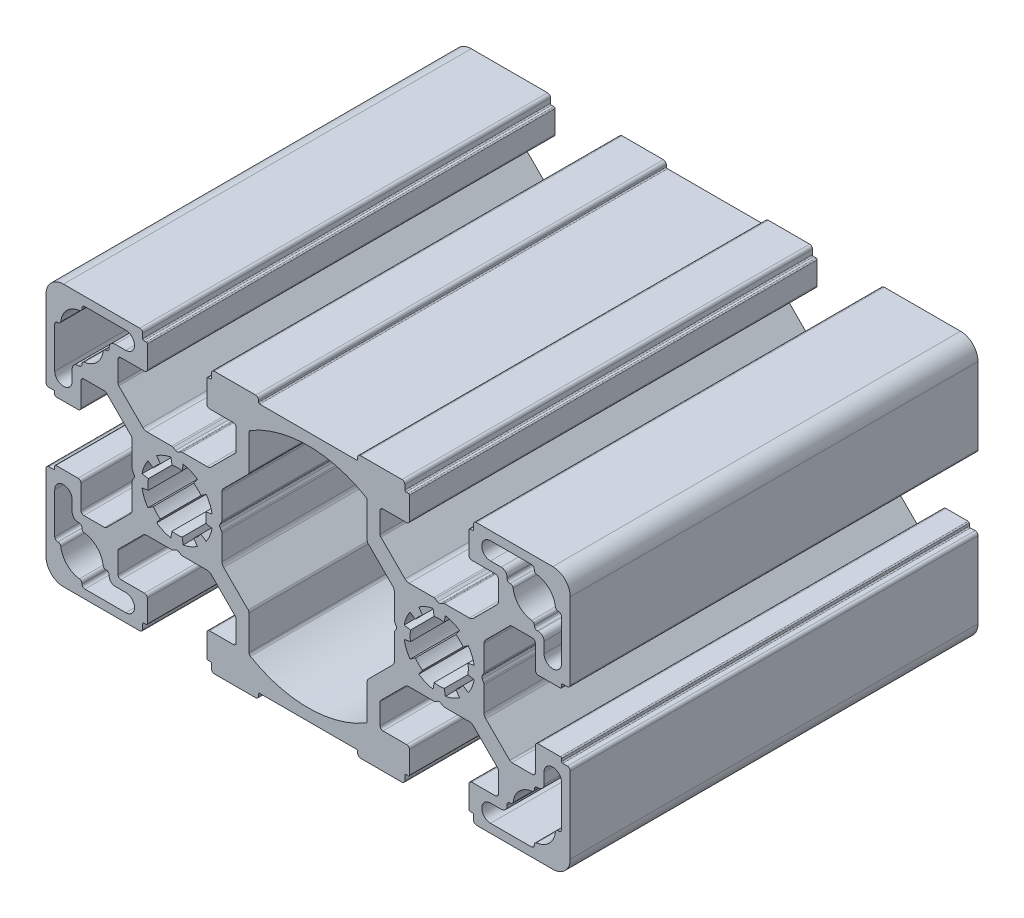
SolidWorks part; units mm, degrees
material "1060 Сплав"
ref_plane "Спереди" through (0, 0, 0) normal (0, 0, 1) x (1, 0, 0)
ref_plane "Сверху" through (0, 0, 0) normal (0, 1, 0) x (1, 0, 0)
ref_plane "Справа" through (0, 0, 0) normal (1, 0, 0) x (0, 0, -1)
sketch "Эскиз1" plane through (0, 0, 0) normal (0, 0, 1) x (1, 0, 0)
  line L0 (-48.4414, 51.0481) -> (-48.4414, 44.0311)
  line L1 (-43.2664, 14.2231) -> (-36.2493, 14.2231)
  line L2 (-35.1419, 36.1522) -> (-35.1419, 40.3881)
  line L3 (-21.8414, 51.7231) -> (-17.7914, 51.7231)
  line L4 (-15.0914, 49.4623) -> (-15.0914, 45.6589)
  line L5 (-17.2012, 43.3419) -> (-15.2378, 45.3054)
  line L6 (-34.8271, 34.9731) -> (-35.0594, 34.5709)
  line L7 (-30.3093, 39.3189) -> (-30.9402, 40.2199)
  line L8 (-43.9414, 40.8231) -> (-43.9414, 44.8731)
  line L9 (-43.4414, 45.3731) -> (-39.9198, 45.3731)
  line L10 (-49.4414, 41.1231) -> (-48.6414, 41.1231)
  line L11 (-48.2414, 40.3231) -> (-44.4414, 40.3231)
  line L12 (-48.4414, 40.9231) -> (-48.4414, 40.5231)
  line L13 (-49.4414, 41.1231) -> (-48.6414, 41.1231)
  line L14 (-23.3456, 38.091) -> (-22.4445, 38.7219)
  line L15 (-23.3456, 38.091) -> (-22.4445, 38.7219)
  line L16 (-48.4414, 40.9231) -> (-48.4414, 40.5231)
  line L17 (-35.5602, 45.4633) -> (-33.3134, 43.2165)
  line L18 (-26.5123, 42.9236) -> (-22.2764, 42.9236)
  line L19 (-49.9414, 41.6231) -> (-49.9414, 54.7231)
  line L20 (-17.2914, 51.2231) -> (-17.2914, 47.7015)
  line L21 (-27.1914, 42.6089) -> (-26.7623, 42.8566)
  line L22 (11.9586, 18.7231) -> (7.9086, 18.7231)
  line L23 (-33.8414, 57.7231) -> (-46.9414, 57.7231)
  line L24 (-21.0414, 57.7231) -> (-13.9414, 57.7231)
  line L25 (-37.6815, 43.3419) -> (-39.5662, 45.2267)
  line L26 (-33.1414, 56.2231) -> (-32.7414, 56.2231)
  line L27 (-34.8271, 35.4731) -> (-35.0749, 35.9022)
  line L28 (-27.6914, 42.6089) -> (-28.1205, 42.8566)
  line L29 (-33.3414, 57.2231) -> (-33.3414, 56.4231)
  line L30 (-33.1414, 56.2231) -> (-32.7414, 56.2231)
  line L31 (-32.5414, 56.0231) -> (-32.5414, 52.2231)
  line L32 (-33.3414, 57.2231) -> (-33.3414, 56.4231)
  line L33 (-35.5602, 45.4633) -> (-37.4449, 47.348)
  line L34 (-33.0414, 51.7231) -> (-37.0914, 51.7231)
  line L35 (-37.6815, 43.3419) -> (-35.4347, 41.0952)
  line L36 (3.3586, 56.7231) -> (-13.2414, 56.7231)
  line L37 (-39.6466, 51.5481) -> (-39.5914, 51.5481)
  line L38 (-47.8861, 51.5481) -> (-47.9414, 51.5481)
  line L39 (-13.4414, 56.9231) -> (-13.4414, 57.2231)
  line L40 (-39.0914, 52.0481) -> (-39.0914, 52.2231)
  line L41 (-45.4414, 45.8731) -> (-45.4414, 44.0311)
  line L42 (-44.2664, 46.8731) -> (-44.4414, 46.8731)
  line L43 (-15.0914, 51.5901) -> (-15.0914, 49.4623)
  line L44 (-43.7664, 47.4284) -> (-43.7664, 47.3731)
  line L45 (38.5586, 19.3981) -> (38.5586, 26.4152)
  line L46 (-17.2012, 43.3419) -> (-19.448, 41.0952)
  line L47 (-27.1914, 42.6089) -> (-26.7891, 42.8411)
  line L48 (-28.3705, 42.9236) -> (-32.6063, 42.9236)
  line L49 (-21.8414, 51.7231) -> (-17.7914, 51.7231)
  line L50 (-19.3226, 45.4633) -> (-17.4378, 47.348)
  line L51 (-21.5414, 57.2231) -> (-21.5414, 56.4231)
  line L52 (-22.3414, 56.0231) -> (-22.3414, 52.2231)
  line L53 (-28.3705, 27.5226) -> (-32.6063, 27.5226)
  line L54 (-21.7414, 56.2231) -> (-22.1414, 56.2231)
  line L55 (-21.5414, 57.2231) -> (-21.5414, 56.4231)
  line L56 (-27.6914, 27.8374) -> (-28.1205, 27.5896)
  line L57 (-21.7414, 56.2231) -> (-22.1414, 56.2231)
  line L58 (-21.7414, 14.2231) -> (-22.1414, 14.2231)
  line L59 (-21.5414, 13.2231) -> (-21.5414, 14.0231)
  line L60 (-21.7414, 14.2231) -> (-22.1414, 14.2231)
  line L61 (-37.5914, 51.2231) -> (-37.5914, 47.7015)
  line L62 (-19.3226, 45.4633) -> (-21.5693, 43.2165)
  line L63 (-27.1914, 27.8374) -> (-26.7623, 27.5896)
  line L64 (-22.3414, 14.4231) -> (-22.3414, 18.2231)
  line L65 (-27.6914, 27.8374) -> (-28.0936, 27.6051)
  line L66 (-21.5414, 13.2231) -> (-21.5414, 14.0231)
  line L67 (-19.3226, 24.983) -> (-17.4378, 23.0982)
  line L68 (-21.8414, 18.7231) -> (-17.7914, 18.7231)
  line L69 (5.2086, 20.9839) -> (5.2086, 24.7873)
  line L70 (7.4086, 19.2231) -> (7.4086, 22.7447)
  line L71 (11.1586, 12.7231) -> (4.0586, 12.7231)
  line L72 (-28.3705, 42.9236) -> (-32.6063, 42.9236)
  line L73 (-24.5735, 39.3189) -> (-23.9426, 40.2199)
  line L74 (-19.7409, 36.1522) -> (-19.7409, 40.3881)
  line L75 (-26.5123, 27.5226) -> (-22.2764, 27.5226)
  line L76 (3.5586, 13.5231) -> (3.5586, 13.2231)
  line L77 (-33.0414, 18.7231) -> (-37.0914, 18.7231)
  line L78 (-43.7664, 14.7784) -> (-43.7664, 14.7231)
  line L79 (-23.3456, 32.3552) -> (-22.4445, 31.7243)
  line L80 (-24.5735, 31.1274) -> (-23.9426, 30.2263)
  line L81 (-38.0914, 17.2231) -> (-36.2493, 17.2231)
  line L82 (-23.3456, 32.3552) -> (-22.4445, 31.7243)
  line L83 (-24.5735, 31.1274) -> (-23.9426, 30.2263)
  line L84 (-26.5731, 30.2991) -> (-26.3821, 29.2158)
  line L85 (-26.5731, 30.2991) -> (-26.3821, 29.2158)
  line L86 (-28.3096, 30.2991) -> (-28.5006, 29.2158)
  line L87 (-31.5371, 32.3552) -> (-32.4382, 31.7243)
  line L88 (-28.3096, 30.2991) -> (-28.5006, 29.2158)
  line L89 (-31.5371, 32.3552) -> (-32.4382, 31.7243)
  line L90 (5.2086, 18.8562) -> (5.2086, 20.9839)
  line L91 (-24.5735, 31.1274) -> (-23.9426, 30.2263)
  line L92 (-28.3705, 27.5226) -> (-32.6063, 27.5226)
  line L93 (-17.2914, 19.2231) -> (-17.2914, 22.7447)
  line L94 (-17.2012, 27.1043) -> (-15.2378, 25.1409)
  line L95 (-15.0914, 20.9839) -> (-15.0914, 24.7873)
  line L96 (-21.8414, 18.7231) -> (-17.7914, 18.7231)
  line L97 (20.4265, 31.1274) -> (21.0574, 30.2263)
  line L98 (34.0586, 29.6231) -> (34.0586, 25.5731)
  line L99 (-19.3226, 24.983) -> (-21.5693, 27.2297)
  line L100 (-34.8271, 34.9731) -> (-35.0749, 34.544)
  line L101 (-37.5914, 19.2231) -> (-37.5914, 22.7447)
  line L102 (20.4265, 31.1274) -> (21.0574, 30.2263)
  line L103 (33.5586, 25.0731) -> (30.0371, 25.0731)
  line L104 (-17.2012, 27.1043) -> (-15.3165, 25.2196)
  line L105 (39.5586, 29.3231) -> (38.7586, 29.3231)
  line L106 (-19.7409, 34.294) -> (-19.7409, 30.0582)
  line L107 (38.3586, 30.1231) -> (34.5586, 30.1231)
  line L108 (38.5586, 29.5231) -> (38.5586, 29.9231)
  line L109 (-20.0556, 35.4731) -> (-19.8234, 35.8754)
  line L110 (39.5586, 29.3231) -> (38.7586, 29.3231)
  line L111 (13.4629, 32.3552) -> (12.5618, 31.7243)
  line L112 (-35.1419, 34.294) -> (-35.1419, 30.0582)
  line L113 (13.4629, 32.3552) -> (12.5618, 31.7243)
  line L114 (13.4629, 32.3552) -> (12.5618, 31.7243)
  line L115 (-28.3705, 27.5226) -> (-32.6063, 27.5226)
  line L116 (-27.1914, 27.8374) -> (-26.7891, 27.6051)
  line L117 (-17.2012, 27.1043) -> (-19.448, 29.3511)
  line L118 (38.5586, 29.5231) -> (38.5586, 29.9231)
  line L119 (-43.7664, 23.0179) -> (-43.7664, 23.0731)
  line L120 (-20.0556, 34.9731) -> (-19.8079, 34.544)
  line L121 (25.6774, 24.983) -> (23.4307, 27.2297)
  line L122 (-44.2664, 23.5731) -> (-44.4414, 23.5731)
  line L123 (-45.4414, 24.5731) -> (-45.4414, 26.4152)
  line L124 (-39.0914, 18.3981) -> (-39.0914, 18.2231)
  line L125 (9.8581, 36.1522) -> (9.8581, 40.3881)
  line L126 (-47.8861, 18.8981) -> (-47.9414, 18.8981)
  line L127 (-31.5371, 38.091) -> (-32.4382, 38.7219)
  line L128 (-28.3096, 40.1472) -> (-28.5006, 41.2304)
  line L129 (-26.5731, 40.1472) -> (-26.3821, 41.2304)
  line L130 (-38.0914, 53.2231) -> (-36.2493, 53.2231)
  line L131 (-32.3654, 34.3549) -> (-33.4487, 34.1639)
  line L132 (-32.3654, 36.0914) -> (-33.4487, 36.2824)
  line L133 (-26.5731, 30.2991) -> (-26.3821, 29.2158)
  line L134 (-28.3096, 30.2991) -> (-28.5006, 29.2158)
  line L135 (-30.3093, 31.1274) -> (-30.9402, 30.2263)
  line L136 (-31.5371, 32.3552) -> (-32.4382, 31.7243)
  line L137 (-32.3654, 34.3549) -> (-33.4487, 34.1639)
  line L138 (-32.3654, 36.0914) -> (-33.4487, 36.2824)
  line L139 (-24.5735, 39.3189) -> (-23.9426, 40.2199)
  line L140 (-23.3456, 38.091) -> (-22.4445, 38.7219)
  line L141 (-22.5173, 36.0914) -> (-21.434, 36.2824)
  line L142 (-22.5173, 34.3549) -> (-21.434, 34.1639)
  line L143 (-23.3456, 32.3552) -> (-22.4445, 31.7243)
  line L144 (-24.5735, 31.1274) -> (-23.9426, 30.2263)
  line L145 (-43.7664, 55.6679) -> (-43.7664, 55.7231)
  line L146 (-39.6466, 18.8981) -> (-39.5914, 18.8981)
  line L147 (-33.0414, 51.7231) -> (-37.0914, 51.7231)
  line L148 (-43.2664, 56.2231) -> (-36.2493, 56.2231)
  line L149 (16.6295, 27.5226) -> (12.3937, 27.5226)
  line L150 (-37.6815, 27.1043) -> (-35.4347, 29.3511)
  line L151 (-33.0414, 18.7231) -> (-37.0914, 18.7231)
  line L152 (-35.5602, 24.983) -> (-37.4449, 23.0982)
  line L153 (-33.3414, 13.2231) -> (-33.3414, 14.0231)
  line L154 (-32.5414, 14.4231) -> (-32.5414, 18.2231)
  line L155 (-33.1414, 14.2231) -> (-32.7414, 14.2231)
  line L156 (-33.3414, 13.2231) -> (-33.3414, 14.0231)
  line L157 (-27.6914, 27.8374) -> (-28.1205, 27.5896)
  line L158 (-33.1414, 14.2231) -> (-32.7414, 14.2231)
  line L159 (-37.6815, 27.1043) -> (-39.5662, 25.2196)
  line L160 (40.0586, 28.8231) -> (40.0586, 15.7231)
  line L161 (-33.8414, 12.7231) -> (-46.9414, 12.7231)
  line L162 (10.1729, 35.4731) -> (9.9251, 35.9022)
  line L163 (-27.1914, 27.8374) -> (-26.7623, 27.5896)
  line L164 (17.3086, 27.8374) -> (16.8795, 27.5896)
  line L165 (-20.0556, 35.4731) -> (-19.8079, 35.9022)
  line L166 (-49.9414, 28.8231) -> (-49.9414, 15.7231)
  line L167 (-26.5123, 27.5226) -> (-22.2764, 27.5226)
  line L168 (-19.7409, 36.1522) -> (-19.7409, 40.3881)
  line L169 (-35.5602, 24.983) -> (-33.3134, 27.2297)
  line L170 (-48.4414, 29.5231) -> (-48.4414, 29.9231)
  line L171 (-23.3456, 32.3552) -> (-22.4445, 31.7243)
  line L172 (-23.3456, 32.3552) -> (-22.4445, 31.7243)
  line L173 (-23.3456, 32.3552) -> (-22.4445, 31.7243)
  line L174 (-49.4414, 29.3231) -> (-48.6414, 29.3231)
  line L175 (-48.4414, 29.5231) -> (-48.4414, 29.9231)
  line L176 (-48.2414, 30.1231) -> (-44.4414, 30.1231)
  line L177 (-49.4414, 29.3231) -> (-48.6414, 29.3231)
  line L178 (-43.4414, 25.0731) -> (-39.9198, 25.0731)
  line L179 (-30.3093, 31.1274) -> (-30.9402, 30.2263)
  line L180 (-43.9414, 29.6231) -> (-43.9414, 25.5731)
  line L181 (-30.3093, 31.1274) -> (-30.9402, 30.2263)
  line L182 (23.9586, 12.7231) -> (37.0586, 12.7231)
  line L183 (27.7988, 27.1043) -> (29.6835, 25.2196)
  line L184 (23.2586, 14.2231) -> (22.8586, 14.2231)
  line L185 (17.8086, 27.8374) -> (18.2377, 27.5896)
  line L186 (-48.4414, 19.3981) -> (-48.4414, 26.4152)
  line L187 (23.4586, 13.2231) -> (23.4586, 14.0231)
  line L188 (23.2586, 14.2231) -> (22.8586, 14.2231)
  line L189 (22.6586, 14.4231) -> (22.6586, 18.2231)
  line L190 (23.4586, 13.2231) -> (23.4586, 14.0231)
  line L191 (25.6774, 24.983) -> (27.5622, 23.0982)
  line L192 (23.1586, 18.7231) -> (27.2086, 18.7231)
  line L193 (27.7988, 27.1043) -> (25.552, 29.3511)
  line L194 (33.3836, 56.2231) -> (26.3666, 56.2231)
  line L195 (23.1586, 51.7231) -> (27.2086, 51.7231)
  line L196 (29.7639, 18.8981) -> (29.7086, 18.8981)
  line L197 (33.8836, 55.6679) -> (33.8836, 55.7231)
  line L198 (14.6907, 31.1274) -> (14.0598, 30.2263)
  line L199 (13.4629, 32.3552) -> (12.5618, 31.7243)
  line L200 (12.6346, 34.3549) -> (11.5513, 34.1639)
  line L201 (12.6346, 36.0914) -> (11.5513, 36.2824)
  line L202 (13.4629, 38.091) -> (12.5618, 38.7219)
  line L203 (14.6907, 39.3189) -> (14.0598, 40.2199)
  line L204 (22.4827, 36.0914) -> (23.566, 36.2824)
  line L205 (22.4827, 34.3549) -> (23.566, 34.1639)
  line L206 (21.6544, 32.3552) -> (22.5555, 31.7243)
  line L207 (20.4265, 31.1274) -> (21.0574, 30.2263)
  line L208 (18.4269, 30.2991) -> (18.6179, 29.2158)
  line L209 (16.6904, 30.2991) -> (16.4994, 29.2158)
  line L210 (22.4827, 36.0914) -> (23.566, 36.2824)
  line L211 (22.4827, 34.3549) -> (23.566, 34.1639)
  line L212 (28.2086, 53.2231) -> (26.3666, 53.2231)
  line L213 (16.6904, 40.1472) -> (16.4994, 41.2304)
  line L214 (18.4269, 40.1472) -> (18.6179, 41.2304)
  line L215 (21.6544, 38.091) -> (22.5555, 38.7219)
  line L216 (38.0034, 18.8981) -> (38.0586, 18.8981)
  line L217 (29.2086, 18.3981) -> (29.2086, 18.2231)
  line L218 (35.5586, 24.5731) -> (35.5586, 26.4152)
  line L219 (34.3836, 23.5731) -> (34.5586, 23.5731)
  line L220 (10.1729, 34.9731) -> (9.9251, 34.544)
  line L221 (33.8836, 23.0179) -> (33.8836, 23.0731)
  line L222 (7.3185, 27.1043) -> (9.5653, 29.3511)
  line L223 (17.3086, 27.8374) -> (16.9064, 27.6051)
  line L224 (18.4877, 27.5226) -> (22.7236, 27.5226)
  line L225 (25.2591, 34.294) -> (25.2591, 30.0582)
  line L226 (10.1729, 35.4731) -> (9.9406, 35.8754)
  line L227 (9.8581, 34.294) -> (9.8581, 30.0582)
  line L228 (7.3185, 27.1043) -> (5.4338, 25.2196)
  line L229 (27.7086, 19.2231) -> (27.7086, 22.7447)
  line L230 (24.9444, 34.9731) -> (25.1921, 34.544)
  line L231 (9.4398, 24.983) -> (11.6866, 27.2297)
  line L232 (11.9586, 18.7231) -> (7.9086, 18.7231)
  line L233 (5.2086, 20.9839) -> (5.2086, 24.7873)
  line L234 (7.3185, 27.1043) -> (5.3551, 25.1409)
  line L235 (7.4086, 19.2231) -> (7.4086, 22.7447)
  line L236 (18.4877, 27.5226) -> (22.7236, 27.5226)
  line L237 (14.6907, 31.1274) -> (14.0598, 30.2263)
  line L238 (21.6544, 32.3552) -> (22.5555, 31.7243)
  line L239 (18.4269, 30.2991) -> (18.6179, 29.2158)
  line L240 (21.6544, 32.3552) -> (22.5555, 31.7243)
  line L241 (18.4269, 30.2991) -> (18.6179, 29.2158)
  line L242 (16.6904, 30.2991) -> (16.4994, 29.2158)
  line L243 (16.6904, 30.2991) -> (16.4994, 29.2158)
  line L244 (14.6907, 31.1274) -> (14.0598, 30.2263)
  line L245 (13.4629, 32.3552) -> (12.5618, 31.7243)
  line L246 (28.2086, 17.2231) -> (26.3666, 17.2231)
  line L247 (14.6907, 31.1274) -> (14.0598, 30.2263)
  line L248 (13.4629, 32.3552) -> (12.5618, 31.7243)
  line L249 (33.8836, 14.7784) -> (33.8836, 14.7231)
  line L250 (23.1586, 18.7231) -> (27.2086, 18.7231)
  line L251 (11.9586, 18.7231) -> (7.9086, 18.7231)
  line L252 (16.6295, 27.5226) -> (12.3937, 27.5226)
  line L253 (9.8581, 36.1522) -> (9.8581, 40.3881)
  line L254 (14.6907, 39.3189) -> (14.0598, 40.2199)
  line L255 (18.4877, 42.9236) -> (22.7236, 42.9236)
  line L256 (9.4398, 24.983) -> (7.5551, 23.0982)
  line L257 (11.6586, 13.2231) -> (11.6586, 14.0231)
  line L258 (11.9586, 18.7231) -> (7.9086, 18.7231)
  line L259 (9.4398, 24.983) -> (7.5551, 23.0982)
  line L260 (11.6586, 13.2231) -> (11.6586, 14.0231)
  line L261 (17.8086, 27.8374) -> (18.2109, 27.6051)
  line L262 (12.4586, 14.4231) -> (12.4586, 18.2231)
  line L263 (17.3086, 27.8374) -> (16.8795, 27.5896)
  line L264 (9.4398, 45.4633) -> (11.6866, 43.2165)
  line L265 (27.7086, 51.2231) -> (27.7086, 47.7015)
  line L266 (11.8586, 14.2231) -> (12.2586, 14.2231)
  line L267 (11.6586, 13.2231) -> (11.6586, 14.0231)
  line L268 (11.8586, 14.2231) -> (12.2586, 14.2231)
  line L269 (11.8586, 56.2231) -> (12.2586, 56.2231)
  line L270 (17.8086, 27.8374) -> (18.2377, 27.5896)
  line L271 (11.6586, 57.2231) -> (11.6586, 56.4231)
  line L272 (11.8586, 56.2231) -> (12.2586, 56.2231)
  line L273 (18.4877, 27.5226) -> (22.7236, 27.5226)
  line L274 (12.4586, 56.0231) -> (12.4586, 52.2231)
  line L275 (11.6586, 57.2231) -> (11.6586, 56.4231)
  line L276 (9.4398, 45.4633) -> (7.5551, 47.348)
  line L277 (11.9586, 51.7231) -> (7.9086, 51.7231)
  line L278 (18.4877, 42.9236) -> (22.7236, 42.9236)
  line L279 (17.3086, 42.6089) -> (16.9064, 42.8411)
  line L280 (7.3185, 43.3419) -> (9.5653, 41.0952)
  line L281 (33.8836, 47.4284) -> (33.8836, 47.3731)
  line L282 (5.2086, 51.5901) -> (5.2086, 49.4623)
  line L283 (34.3836, 46.8731) -> (34.5586, 46.8731)
  line L284 (35.5586, 45.8731) -> (35.5586, 44.0311)
  line L285 (29.2086, 52.0481) -> (29.2086, 52.2231)
  line L286 (3.5586, 56.9231) -> (3.5586, 57.2231)
  line L287 (38.0034, 51.5481) -> (38.0586, 51.5481)
  line L288 (29.7639, 51.5481) -> (29.7086, 51.5481)
  line L289 (27.7988, 43.3419) -> (25.552, 41.0952)
  line L290 (23.1586, 51.7231) -> (27.2086, 51.7231)
  line L291 (25.6774, 45.4633) -> (27.5622, 47.348)
  line L292 (23.4586, 57.2231) -> (23.4586, 56.4231)
  line L293 (22.6586, 56.0231) -> (22.6586, 52.2231)
  line L294 (23.2586, 56.2231) -> (22.8586, 56.2231)
  line L295 (23.4586, 57.2231) -> (23.4586, 56.4231)
  line L296 (17.8086, 42.6089) -> (18.2377, 42.8566)
  line L297 (24.9444, 35.4731) -> (25.1921, 35.9022)
  line L298 (23.2586, 56.2231) -> (22.8586, 56.2231)
  line L299 (27.7988, 43.3419) -> (29.6835, 45.2267)
  line L300 (11.1586, 57.7231) -> (4.0586, 57.7231)
  line L301 (23.9586, 57.7231) -> (37.0586, 57.7231)
  line L302 (17.3086, 42.6089) -> (16.8795, 42.8566)
  line L303 (7.4086, 51.2231) -> (7.4086, 47.7015)
  line L304 (40.0586, 41.6231) -> (40.0586, 54.7231)
  line L305 (16.6295, 42.9236) -> (12.3937, 42.9236)
  line L306 (25.6774, 45.4633) -> (23.4307, 43.2165)
  line L307 (38.5586, 40.9231) -> (38.5586, 40.5231)
  line L308 (13.4629, 38.091) -> (12.5618, 38.7219)
  line L309 (13.4629, 38.091) -> (12.5618, 38.7219)
  line L310 (39.5586, 41.1231) -> (38.7586, 41.1231)
  line L311 (38.5586, 40.9231) -> (38.5586, 40.5231)
  line L312 (38.3586, 40.3231) -> (34.5586, 40.3231)
  line L313 (39.5586, 41.1231) -> (38.7586, 41.1231)
  line L314 (33.5586, 45.3731) -> (30.0371, 45.3731)
  line L315 (34.0586, 40.8231) -> (34.0586, 44.8731)
  line L316 (20.4265, 39.3189) -> (21.0574, 40.2199)
  line L317 (24.9444, 34.9731) -> (25.1766, 34.5709)
  line L318 (7.3185, 43.3419) -> (5.3551, 45.3054)
  line L319 (5.2086, 49.4623) -> (5.2086, 45.6589)
  line L320 (11.9586, 51.7231) -> (7.9086, 51.7231)
  line L321 (25.2591, 36.1522) -> (25.2591, 40.3881)
  line L322 (33.3836, 14.2231) -> (26.3666, 14.2231)
  line L323 (38.5586, 51.0481) -> (38.5586, 44.0311)
  line L325 (12.4586, 14.4231) -> (12.4586, 18.2231)
  line L326 (11.8586, 14.2231) -> (12.2586, 14.2231)
  line L327 (11.6586, 13.2231) -> (11.6586, 14.0231)
  line L328 (11.8586, 14.2231) -> (12.2586, 14.2231)
  line L329 (-21.7414, 14.2231) -> (-22.1414, 14.2231)
  line L330 (-21.5414, 13.2231) -> (-21.5414, 14.0231)
  line L331 (-21.7414, 14.2231) -> (-22.1414, 14.2231)
  line L332 (-22.3414, 14.4231) -> (-22.3414, 18.2231)
  line L333 (-21.5414, 13.2231) -> (-21.5414, 14.0231)
  line L334 (-19.3226, 24.983) -> (-17.4378, 23.0982)
  line L335 (-21.8414, 18.7231) -> (-17.7914, 18.7231)
  line L336 (-15.0914, 18.8562) -> (-15.0914, 20.9839)
  line L337 (-13.4414, 13.5231) -> (-13.4414, 13.2231)
  line L338 (3.3586, 13.7231) -> (-13.2414, 13.7231)
  line L339 (-21.0414, 12.7231) -> (-13.9414, 12.7231)
  line L340 (-17.2914, 19.2231) -> (-17.2914, 22.7447)
  line L341 (-15.0914, 20.9839) -> (-15.0914, 24.7873)
  line L342 (-21.8414, 18.7231) -> (-17.7914, 18.7231)
  arc A0 (-30.3093, 39.3189) -> (-31.5371, 38.091) centre (-27.4414, 35.2231) ccw
  arc A1 (-32.4382, 38.7219) -> (-33.4487, 36.2824) centre (-27.4414, 35.2231) ccw
  arc A2 (-46.9414, 57.7231) -> (-49.9414, 54.7231) centre (-46.9414, 54.7231) ccw
  arc A3 (-39.5662, 45.2267) -> (-39.9198, 45.3731) centre (-39.9198, 44.8731) ccw
  arc A4 (-43.4414, 45.3731) -> (-43.9414, 44.8731) centre (-43.4414, 44.8731) ccw
  arc A5 (-44.4414, 40.3231) -> (-43.9414, 40.8231) centre (-44.4414, 40.8231) ccw
  arc A6 (-49.9414, 41.6231) -> (-49.4414, 41.1231) centre (-49.4414, 41.6231) ccw
  arc A7 (-48.2414, 40.3231) -> (-48.4414, 40.5231) centre (-48.2414, 40.5231) cw
  arc A8 (-48.6414, 41.1231) -> (-48.4414, 40.9231) centre (-48.6414, 40.9231) cw
  arc A9 (-35.4347, 41.0952) -> (-35.1419, 40.3881) centre (-36.1419, 40.3881) cw
  arc A10 (-17.2914, 51.2231) -> (-17.7914, 51.7231) centre (-17.7914, 51.2231) ccw
  arc A11 (-15.2378, 45.3054) -> (-15.0914, 45.6589) centre (-15.5914, 45.6589) ccw
  arc A12 (4.9626, 52.0208) -> (5.2086, 51.5901) centre (4.7086, 51.5901) cw
  arc A13 (-13.4414, 57.2231) -> (-13.9414, 57.7231) centre (-13.9414, 57.2231) ccw
  arc A14 (-13.2414, 56.7231) -> (-13.4414, 56.9231) centre (-13.2414, 56.9231) cw
  arc A15 (-21.5414, 14.0231) -> (-21.7414, 14.2231) centre (-21.7414, 14.0231) ccw
  arc A16 (-35.0749, 34.544) -> (-35.1419, 34.294) centre (-34.6419, 34.294) ccw
  arc A17 (-33.3414, 56.4231) -> (-33.1414, 56.2231) centre (-33.1414, 56.4231) ccw
  arc A18 (-34.8271, 34.9731) -> (-34.8271, 35.4731) centre (-35.2601, 35.2231) ccw
  arc A19 (-49.9414, 41.6231) -> (-49.4414, 41.1231) centre (-49.4414, 41.6231) ccw
  arc A20 (-48.6414, 41.1231) -> (-48.4414, 40.9231) centre (-48.6414, 40.9231) cw
  arc A21 (-33.8414, 57.7231) -> (-33.3414, 57.2231) centre (-33.8414, 57.2231) cw
  arc A22 (-28.1205, 42.8566) -> (-28.3705, 42.9236) centre (-28.3705, 42.4236) ccw
  arc A23 (-21.0414, 12.7231) -> (-21.5414, 13.2231) centre (-21.0414, 13.2231) cw
  arc A24 (-27.1914, 42.6089) -> (-27.6914, 42.6089) centre (-27.4414, 43.0419) cw
  arc A25 (-33.3414, 56.4231) -> (-33.1414, 56.2231) centre (-33.1414, 56.4231) ccw
  arc A26 (-32.5414, 56.0231) -> (-32.7414, 56.2231) centre (-32.7414, 56.0231) ccw
  arc A27 (-33.8414, 57.7231) -> (-33.3414, 57.2231) centre (-33.8414, 57.2231) cw
  arc A28 (-32.5414, 52.2231) -> (-33.0414, 51.7231) centre (-33.0414, 52.2231) cw
  arc A29 (-37.5914, 51.2231) -> (-37.0914, 51.7231) centre (-37.0914, 51.2231) cw
  arc A30 (-33.3134, 43.2165) -> (-32.6063, 42.9236) centre (-32.6063, 43.9236) ccw
  arc A31 (-43.3266, 47.9247) -> (-40.143, 51.1084) centre (-43.7664, 51.5481) ccw
  arc A32 (-48.4414, 44.0311) -> (-45.4414, 44.0311) centre (-46.9414, 44.0311) ccw
  arc A33 (-44.4414, 46.8731) -> (-45.4414, 45.8731) centre (-44.4414, 45.8731) ccw
  arc A34 (-47.9414, 51.5481) -> (-48.4414, 51.0481) centre (-47.9414, 51.0481) ccw
  arc A35 (-47.8861, 51.5481) -> (-47.3898, 51.9879) centre (-47.8861, 52.0481) ccw
  arc A36 (-43.7664, 47.4284) -> (-43.3266, 47.9247) centre (-43.2664, 47.4284) cw
  arc A37 (-21.5414, 14.0231) -> (-21.7414, 14.2231) centre (-21.7414, 14.0231) ccw
  arc A38 (-22.3414, 14.4231) -> (-22.1414, 14.2231) centre (-22.1414, 14.4231) ccw
  arc A39 (-21.0414, 12.7231) -> (-21.5414, 13.2231) centre (-21.0414, 13.2231) cw
  arc A40 (-17.4378, 47.348) -> (-17.2914, 47.7015) centre (-17.7914, 47.7015) ccw
  arc A41 (-22.3414, 18.2231) -> (-21.8414, 18.7231) centre (-21.8414, 18.2231) cw
  arc A42 (-17.2914, 19.2231) -> (-17.7914, 18.7231) centre (-17.7914, 19.2231) cw
  arc A43 (-26.7623, 42.8566) -> (-26.5123, 42.9236) centre (-26.5123, 42.4236) cw
  arc A44 (-37.4449, 47.348) -> (-37.5914, 47.7015) centre (-37.0914, 47.7015) cw
  arc A45 (-17.4378, 23.0982) -> (-17.2914, 22.7447) centre (-17.7914, 22.7447) cw
  arc A46 (4.9626, 18.4254) -> (-14.8453, 18.4254) centre (-4.9414, 35.2231) cw
  arc A47 (7.4086, 19.2231) -> (7.9086, 18.7231) centre (7.9086, 19.2231) ccw
  arc A48 (-26.7623, 27.5896) -> (-26.5123, 27.5226) centre (-26.5123, 28.0226) ccw
  arc A49 (5.3551, 25.1409) -> (5.2086, 24.7873) centre (5.7086, 24.7873) ccw
  arc A50 (-21.5693, 43.2165) -> (-22.2764, 42.9236) centre (-22.2764, 43.9236) cw
  arc A51 (-27.6914, 27.8374) -> (-27.1914, 27.8374) centre (-27.4414, 27.4044) cw
  arc A52 (-17.2914, 51.2231) -> (-17.7914, 51.7231) centre (-17.7914, 51.2231) ccw
  arc A53 (-22.3414, 52.2231) -> (-21.8414, 51.7231) centre (-21.8414, 52.2231) ccw
  arc A54 (-21.0414, 57.7231) -> (-21.5414, 57.2231) centre (-21.0414, 57.2231) ccw
  arc A55 (-22.3414, 56.0231) -> (-22.1414, 56.2231) centre (-22.1414, 56.0231) cw
  arc A56 (-21.5414, 56.4231) -> (-21.7414, 56.2231) centre (-21.7414, 56.4231) cw
  arc A57 (-21.0414, 57.7231) -> (-21.5414, 57.2231) centre (-21.0414, 57.2231) ccw
  arc A58 (-28.1205, 27.5896) -> (-28.3705, 27.5226) centre (-28.3705, 28.0226) cw
  arc A59 (-15.2378, 25.1409) -> (-15.0914, 24.7873) centre (-15.5914, 24.7873) cw
  arc A60 (-17.2914, 19.2231) -> (-17.7914, 18.7231) centre (-17.7914, 19.2231) cw
  arc A61 (-21.5414, 56.4231) -> (-21.7414, 56.2231) centre (-21.7414, 56.4231) cw
  arc A62 (-19.448, 41.0952) -> (-19.7409, 40.3881) centre (-18.7409, 40.3881) ccw
  arc A63 (20.4265, 31.1274) -> (21.6544, 32.3552) centre (17.5586, 35.2231) ccw
  arc A64 (37.0586, 12.7231) -> (40.0586, 15.7231) centre (37.0586, 15.7231) ccw
  arc A65 (29.6835, 25.2196) -> (30.0371, 25.0731) centre (30.0371, 25.5731) ccw
  arc A66 (33.5586, 25.0731) -> (34.0586, 25.5731) centre (33.5586, 25.5731) ccw
  arc A67 (-19.8079, 35.9022) -> (-19.7409, 36.1522) centre (-20.2409, 36.1522) ccw
  arc A68 (34.5586, 30.1231) -> (34.0586, 29.6231) centre (34.5586, 29.6231) ccw
  arc A69 (40.0586, 28.8231) -> (39.5586, 29.3231) centre (39.5586, 28.8231) ccw
  arc A70 (38.3586, 30.1231) -> (38.5586, 29.9231) centre (38.3586, 29.9231) cw
  arc A71 (-22.4445, 38.7219) -> (-21.434, 36.2824) centre (-27.4414, 35.2231) cw
  arc A72 (-20.0556, 35.4731) -> (-20.0556, 34.9731) centre (-19.6226, 35.2231) ccw
  arc A73 (-24.5735, 39.3189) -> (-23.3456, 38.091) centre (-27.4414, 35.2231) cw
  arc A74 (-37.5914, 19.2231) -> (-37.0914, 18.7231) centre (-37.0914, 19.2231) ccw
  arc A75 (-36.2493, 14.2231) -> (-36.2493, 17.2231) centre (-36.2493, 15.7231) ccw
  arc A76 (-39.0914, 18.2231) -> (-38.0914, 17.2231) centre (-38.0914, 18.2231) ccw
  arc A77 (-43.7664, 14.7231) -> (-43.2664, 14.2231) centre (-43.2664, 14.7231) ccw
  arc A78 (-43.7664, 14.7784) -> (-44.2061, 15.2747) centre (-44.2664, 14.7784) ccw
  arc A79 (-39.6466, 18.8981) -> (-40.143, 19.3379) centre (-39.6466, 19.3981) cw
  arc A80 (-39.5914, 18.8981) -> (-39.0914, 18.3981) centre (-39.5914, 18.3981) cw
  arc A81 (-44.2061, 15.2747) -> (-47.3898, 18.4584) centre (-43.7664, 18.8981) cw
  arc A82 (-43.7664, 23.0731) -> (-44.2664, 23.5731) centre (-44.2664, 23.0731) ccw
  arc A83 (-46.9414, 12.7231) -> (-49.9414, 15.7231) centre (-46.9414, 15.7231) cw
  arc A84 (-23.3456, 32.3552) -> (-24.5735, 31.1274) centre (-27.4414, 35.2231) cw
  arc A85 (-23.9426, 30.2263) -> (-26.3821, 29.2158) centre (-27.4414, 35.2231) cw
  arc A86 (-26.5731, 30.2991) -> (-28.3096, 30.2991) centre (-27.4414, 35.2231) cw
  arc A87 (-28.5006, 29.2158) -> (-30.9402, 30.2263) centre (-27.4414, 35.2231) cw
  arc A88 (-23.9426, 30.2263) -> (-26.3821, 29.2158) centre (-27.4414, 35.2231) cw
  arc A89 (-26.5731, 30.2991) -> (-28.3096, 30.2991) centre (-27.4414, 35.2231) cw
  arc A90 (-28.5006, 29.2158) -> (-30.9402, 30.2263) centre (-27.4414, 35.2231) cw
  arc A91 (-24.5735, 31.1274) -> (-23.3456, 32.3552) centre (-27.4414, 35.2231) ccw
  arc A92 (-19.8079, 34.544) -> (-19.7409, 34.294) centre (-20.2409, 34.294) cw
  arc A93 (38.7586, 29.3231) -> (38.5586, 29.5231) centre (38.7586, 29.5231) cw
  arc A94 (25.552, 29.3511) -> (25.2591, 30.0582) centre (26.2591, 30.0582) cw
  arc A95 (23.4586, 14.0231) -> (23.2586, 14.2231) centre (23.2586, 14.0231) ccw
  arc A96 (40.0586, 28.8231) -> (39.5586, 29.3231) centre (39.5586, 28.8231) ccw
  arc A97 (38.7586, 29.3231) -> (38.5586, 29.5231) centre (38.7586, 29.5231) cw
  arc A98 (23.9586, 12.7231) -> (23.4586, 13.2231) centre (23.9586, 13.2231) cw
  arc A99 (18.2377, 27.5896) -> (18.4877, 27.5226) centre (18.4877, 28.0226) ccw
  arc A100 (-19.448, 29.3511) -> (-19.7409, 30.0582) centre (-18.7409, 30.0582) cw
  arc A101 (17.3086, 27.8374) -> (17.8086, 27.8374) centre (17.5586, 27.4044) cw
  arc A102 (-35.0749, 35.9022) -> (-35.1419, 36.1522) centre (-34.6419, 36.1522) cw
  arc A103 (23.4586, 14.0231) -> (23.2586, 14.2231) centre (23.2586, 14.0231) ccw
  arc A104 (22.6586, 14.4231) -> (22.8586, 14.2231) centre (22.8586, 14.4231) ccw
  arc A105 (23.9586, 12.7231) -> (23.4586, 13.2231) centre (23.9586, 13.2231) cw
  arc A106 (22.6586, 18.2231) -> (23.1586, 18.7231) centre (23.1586, 18.2231) cw
  arc A107 (27.7086, 19.2231) -> (27.2086, 18.7231) centre (27.2086, 19.2231) cw
  arc A108 (23.4307, 27.2297) -> (22.7236, 27.5226) centre (22.7236, 26.5226) ccw
  arc A109 (33.4439, 22.5215) -> (30.2602, 19.3379) centre (33.8836, 18.8981) ccw
  arc A110 (38.5586, 26.4152) -> (35.5586, 26.4152) centre (37.0586, 26.4152) ccw
  arc A111 (-21.5693, 27.2297) -> (-22.2764, 27.5226) centre (-22.2764, 26.5226) ccw
  arc A112 (34.5586, 23.5731) -> (35.5586, 24.5731) centre (34.5586, 24.5731) ccw
  arc A113 (38.0586, 18.8981) -> (38.5586, 19.3981) centre (38.0586, 19.3981) ccw
  arc A114 (-28.5006, 41.2304) -> (-30.9402, 40.2199) centre (-27.4414, 35.2231) ccw
  arc A115 (-26.5731, 40.1472) -> (-28.3096, 40.1472) centre (-27.4414, 35.2231) ccw
  arc A116 (-23.9426, 40.2199) -> (-26.3821, 41.2304) centre (-27.4414, 35.2231) ccw
  arc A117 (-23.3456, 38.091) -> (-24.5735, 39.3189) centre (-27.4414, 35.2231) ccw
  arc A118 (-22.5173, 34.3549) -> (-22.5173, 36.0914) centre (-27.4414, 35.2231) ccw
  arc A119 (-21.434, 36.2824) -> (-22.4445, 38.7219) centre (-27.4414, 35.2231) ccw
  arc A120 (-24.5735, 31.1274) -> (-23.3456, 32.3552) centre (-27.4414, 35.2231) ccw
  arc A121 (-22.4445, 31.7243) -> (-21.434, 34.1639) centre (-27.4414, 35.2231) ccw
  arc A122 (-28.3096, 30.2991) -> (-26.5731, 30.2991) centre (-27.4414, 35.2231) ccw
  arc A123 (-26.3821, 29.2158) -> (-23.9426, 30.2263) centre (-27.4414, 35.2231) ccw
  arc A124 (-31.5371, 32.3552) -> (-30.3093, 31.1274) centre (-27.4414, 35.2231) ccw
  arc A125 (-30.9402, 30.2263) -> (-28.5006, 29.2158) centre (-27.4414, 35.2231) ccw
  arc A126 (-32.3654, 36.0914) -> (-32.3654, 34.3549) centre (-27.4414, 35.2231) ccw
  arc A127 (-33.4487, 34.1639) -> (-32.4382, 31.7243) centre (-27.4414, 35.2231) ccw
  arc A128 (-46.9414, 57.7231) -> (-49.9414, 54.7231) centre (-46.9414, 54.7231) ccw
  arc A129 (-43.7664, 47.3731) -> (-44.2664, 46.8731) centre (-44.2664, 47.3731) cw
  arc A130 (-44.2061, 55.1715) -> (-47.3898, 51.9879) centre (-43.7664, 51.5481) ccw
  arc A131 (-39.5914, 51.5481) -> (-39.0914, 52.0481) centre (-39.5914, 52.0481) ccw
  arc A132 (-39.6466, 51.5481) -> (-40.143, 51.1084) centre (-39.6466, 51.0481) ccw
  arc A133 (-43.7664, 55.6679) -> (-44.2061, 55.1715) centre (-44.2664, 55.6679) cw
  arc A134 (-43.7664, 55.7231) -> (-43.2664, 56.2231) centre (-43.2664, 55.7231) cw
  arc A135 (-39.0914, 52.2231) -> (-38.0914, 53.2231) centre (-38.0914, 52.2231) cw
  arc A136 (-36.2493, 56.2231) -> (-36.2493, 53.2231) centre (-36.2493, 54.7231) cw
  arc A137 (-37.5914, 51.2231) -> (-37.0914, 51.7231) centre (-37.0914, 51.2231) cw
  arc A138 (38.0034, 18.8981) -> (37.507, 18.4584) centre (38.0034, 18.3981) ccw
  arc A139 (33.8836, 23.0179) -> (33.4439, 22.5215) centre (33.3836, 23.0179) cw
  arc A140 (-37.4449, 23.0982) -> (-37.5914, 22.7447) centre (-37.0914, 22.7447) ccw
  arc A141 (-26.7623, 27.5896) -> (-26.5123, 27.5226) centre (-26.5123, 28.0226) ccw
  arc A142 (16.8795, 27.5896) -> (16.6295, 27.5226) centre (16.6295, 28.0226) cw
  arc A143 (27.5622, 23.0982) -> (27.7086, 22.7447) centre (27.2086, 22.7447) cw
  arc A144 (27.7086, 51.2231) -> (27.2086, 51.7231) centre (27.2086, 51.2231) ccw
  arc A145 (26.3666, 56.2231) -> (26.3666, 53.2231) centre (26.3666, 54.7231) ccw
  arc A146 (29.2086, 52.2231) -> (28.2086, 53.2231) centre (28.2086, 52.2231) ccw
  arc A147 (33.8836, 55.7231) -> (33.3836, 56.2231) centre (33.3836, 55.7231) ccw
  arc A148 (-43.7664, 23.0179) -> (-43.3266, 22.5215) centre (-43.2664, 23.0179) ccw
  arc A149 (-47.8861, 18.8981) -> (-47.3898, 18.4584) centre (-47.8861, 18.3981) cw
  arc A150 (-47.9414, 18.8981) -> (-48.4414, 19.3981) centre (-47.9414, 19.3981) cw
  arc A151 (-44.4414, 23.5731) -> (-45.4414, 24.5731) centre (-44.4414, 24.5731) cw
  arc A152 (-48.4414, 26.4152) -> (-45.4414, 26.4152) centre (-46.9414, 26.4152) cw
  arc A153 (-43.3266, 22.5215) -> (-40.143, 19.3379) centre (-43.7664, 18.8981) cw
  arc A154 (-33.3134, 27.2297) -> (-32.6063, 27.5226) centre (-32.6063, 26.5226) cw
  arc A155 (-37.5914, 19.2231) -> (-37.0914, 18.7231) centre (-37.0914, 19.2231) ccw
  arc A156 (-32.5414, 18.2231) -> (-33.0414, 18.7231) centre (-33.0414, 18.2231) ccw
  arc A157 (-33.8414, 12.7231) -> (-33.3414, 13.2231) centre (-33.8414, 13.2231) ccw
  arc A158 (-32.5414, 14.4231) -> (-32.7414, 14.2231) centre (-32.7414, 14.4231) cw
  arc A159 (-33.3414, 14.0231) -> (-33.1414, 14.2231) centre (-33.1414, 14.0231) cw
  arc A160 (-27.1914, 27.8374) -> (-27.6914, 27.8374) centre (-27.4414, 27.4044) ccw
  arc A161 (33.8836, 55.6679) -> (34.3234, 55.1715) centre (34.3836, 55.6679) ccw
  arc A162 (-28.1205, 27.5896) -> (-28.3705, 27.5226) centre (-28.3705, 28.0226) cw
  arc A163 (-33.8414, 12.7231) -> (-33.3414, 13.2231) centre (-33.8414, 13.2231) ccw
  arc A164 (-48.6414, 29.3231) -> (-48.4414, 29.5231) centre (-48.6414, 29.5231) ccw
  arc A165 (-49.9414, 28.8231) -> (-49.4414, 29.3231) centre (-49.4414, 28.8231) cw
  arc A166 (-33.3414, 14.0231) -> (-33.1414, 14.2231) centre (-33.1414, 14.0231) cw
  arc A167 (29.7639, 51.5481) -> (30.2602, 51.1084) centre (29.7639, 51.0481) cw
  arc A168 (29.7086, 51.5481) -> (29.2086, 52.0481) centre (29.7086, 52.0481) cw
  arc A169 (34.3234, 55.1715) -> (37.507, 51.9879) centre (33.8836, 51.5481) cw
  arc A170 (33.8836, 47.3731) -> (34.3836, 46.8731) centre (34.3836, 47.3731) ccw
  arc A171 (37.0586, 57.7231) -> (40.0586, 54.7231) centre (37.0586, 54.7231) cw
  arc A172 (23.566, 34.1639) -> (22.5555, 31.7243) centre (17.5586, 35.2231) cw
  arc A173 (-35.4347, 29.3511) -> (-35.1419, 30.0582) centre (-36.1419, 30.0582) ccw
  arc A174 (-48.6414, 29.3231) -> (-48.4414, 29.5231) centre (-48.6414, 29.5231) ccw
  arc A175 (-48.2414, 30.1231) -> (-48.4414, 29.9231) centre (-48.2414, 29.9231) ccw
  arc A176 (-49.9414, 28.8231) -> (-49.4414, 29.3231) centre (-49.4414, 28.8231) cw
  arc A177 (-44.4414, 30.1231) -> (-43.9414, 29.6231) centre (-44.4414, 29.6231) cw
  arc A178 (-43.4414, 25.0731) -> (-43.9414, 25.5731) centre (-43.4414, 25.5731) cw
  arc A179 (-39.5662, 25.2196) -> (-39.9198, 25.0731) centre (-39.9198, 25.5731) cw
  arc A180 (-46.9414, 12.7231) -> (-49.9414, 15.7231) centre (-46.9414, 15.7231) cw
  arc A181 (-30.3093, 31.1274) -> (-31.5371, 32.3552) centre (-27.4414, 35.2231) cw
  arc A182 (22.4827, 36.0914) -> (22.4827, 34.3549) centre (17.5586, 35.2231) cw
  arc A183 (21.0574, 30.2263) -> (18.6179, 29.2158) centre (17.5586, 35.2231) cw
  arc A184 (21.6544, 32.3552) -> (20.4265, 31.1274) centre (17.5586, 35.2231) cw
  arc A185 (16.4994, 29.2158) -> (14.0598, 30.2263) centre (17.5586, 35.2231) cw
  arc A186 (18.4269, 30.2991) -> (16.6904, 30.2991) centre (17.5586, 35.2231) cw
  arc A187 (12.5618, 31.7243) -> (11.5513, 34.1639) centre (17.5586, 35.2231) cw
  arc A188 (14.6907, 31.1274) -> (13.4629, 32.3552) centre (17.5586, 35.2231) cw
  arc A189 (11.5513, 36.2824) -> (12.5618, 38.7219) centre (17.5586, 35.2231) cw
  arc A190 (12.6346, 34.3549) -> (12.6346, 36.0914) centre (17.5586, 35.2231) cw
  arc A191 (13.4629, 38.091) -> (14.6907, 39.3189) centre (17.5586, 35.2231) cw
  arc A192 (14.0598, 40.2199) -> (16.4994, 41.2304) centre (17.5586, 35.2231) cw
  arc A193 (16.6904, 40.1472) -> (18.4269, 40.1472) centre (17.5586, 35.2231) cw
  arc A194 (18.6179, 41.2304) -> (21.0574, 40.2199) centre (17.5586, 35.2231) cw
  arc A195 (11.6866, 27.2297) -> (12.3937, 27.5226) centre (12.3937, 26.5226) cw
  arc A196 (25.1921, 35.9022) -> (25.2591, 36.1522) centre (24.7591, 36.1522) ccw
  arc A197 (9.5653, 29.3511) -> (9.8581, 30.0582) centre (8.8581, 30.0582) ccw
  arc A198 (9.9251, 34.544) -> (9.8581, 34.294) centre (10.3581, 34.294) ccw
  arc A199 (14.6907, 31.1274) -> (13.4629, 32.3552) centre (17.5586, 35.2231) cw
  arc A200 (18.6179, 29.2158) -> (21.0574, 30.2263) centre (17.5586, 35.2231) ccw
  arc A201 (16.6904, 30.2991) -> (18.4269, 30.2991) centre (17.5586, 35.2231) ccw
  arc A202 (14.0598, 30.2263) -> (16.4994, 29.2158) centre (17.5586, 35.2231) ccw
  arc A203 (18.6179, 29.2158) -> (21.0574, 30.2263) centre (17.5586, 35.2231) ccw
  arc A204 (16.6904, 30.2991) -> (18.4269, 30.2991) centre (17.5586, 35.2231) ccw
  arc A205 (14.0598, 30.2263) -> (16.4994, 29.2158) centre (17.5586, 35.2231) ccw
  arc A206 (13.4629, 32.3552) -> (14.6907, 31.1274) centre (17.5586, 35.2231) ccw
  arc A207 (37.0586, 12.7231) -> (40.0586, 15.7231) centre (37.0586, 15.7231) ccw
  arc A208 (33.8836, 23.0731) -> (34.3836, 23.5731) centre (34.3836, 23.0731) cw
  arc A209 (34.3234, 15.2747) -> (37.507, 18.4584) centre (33.8836, 18.8981) ccw
  arc A210 (29.7086, 18.8981) -> (29.2086, 18.3981) centre (29.7086, 18.3981) ccw
  arc A211 (29.7639, 18.8981) -> (30.2602, 19.3379) centre (29.7639, 19.3981) ccw
  arc A212 (33.8836, 14.7784) -> (34.3234, 15.2747) centre (34.3836, 14.7784) cw
  arc A213 (33.8836, 14.7231) -> (33.3836, 14.2231) centre (33.3836, 14.7231) cw
  arc A214 (29.2086, 18.2231) -> (28.2086, 17.2231) centre (28.2086, 18.2231) cw
  arc A215 (26.3666, 14.2231) -> (26.3666, 17.2231) centre (26.3666, 15.7231) cw
  arc A216 (27.7086, 19.2231) -> (27.2086, 18.7231) centre (27.2086, 19.2231) cw
  arc A217 (14.6907, 39.3189) -> (13.4629, 38.091) centre (17.5586, 35.2231) ccw
  arc A218 (10.1729, 35.4731) -> (10.1729, 34.9731) centre (9.7399, 35.2231) cw
  arc A219 (12.5618, 38.7219) -> (11.5513, 36.2824) centre (17.5586, 35.2231) ccw
  arc A220 (9.9251, 35.9022) -> (9.8581, 36.1522) centre (10.3581, 36.1522) cw
  arc A221 (9.5653, 41.0952) -> (9.8581, 40.3881) centre (8.8581, 40.3881) cw
  arc A222 (11.6586, 56.4231) -> (11.8586, 56.2231) centre (11.8586, 56.4231) ccw
  arc A223 (7.4086, 19.2231) -> (7.9086, 18.7231) centre (7.9086, 19.2231) ccw
  arc A224 (5.3551, 25.1409) -> (5.2086, 24.7873) centre (5.7086, 24.7873) ccw
  arc A225 (18.2377, 27.5896) -> (18.4877, 27.5226) centre (18.4877, 28.0226) ccw
  arc A226 (11.1586, 57.7231) -> (11.6586, 57.2231) centre (11.1586, 57.2231) cw
  arc A227 (11.6586, 56.4231) -> (11.8586, 56.2231) centre (11.8586, 56.4231) ccw
  arc A228 (12.4586, 56.0231) -> (12.2586, 56.2231) centre (12.2586, 56.0231) ccw
  arc A229 (11.1586, 57.7231) -> (11.6586, 57.2231) centre (11.1586, 57.2231) cw
  arc A230 (12.4586, 52.2231) -> (11.9586, 51.7231) centre (11.9586, 52.2231) cw
  arc A231 (7.4086, 51.2231) -> (7.9086, 51.7231) centre (7.9086, 51.2231) cw
  arc A232 (17.8086, 27.8374) -> (17.3086, 27.8374) centre (17.5586, 27.4044) ccw
  arc A233 (11.6866, 43.2165) -> (12.3937, 42.9236) centre (12.3937, 43.9236) ccw
  arc A234 (-14.8453, 18.4254) -> (-15.0914, 18.8562) centre (-14.5914, 18.8562) cw
  arc A235 (16.8795, 27.5896) -> (16.6295, 27.5226) centre (16.6295, 28.0226) cw
  arc A236 (3.5586, 13.2231) -> (4.0586, 12.7231) centre (4.0586, 13.2231) ccw
  arc A237 (3.3586, 13.7231) -> (3.5586, 13.5231) centre (3.3586, 13.5231) cw
  arc A238 (7.5551, 23.0982) -> (7.4086, 22.7447) centre (7.9086, 22.7447) ccw
  arc A239 (27.5622, 47.348) -> (27.7086, 47.7015) centre (27.2086, 47.7015) ccw
  arc A240 (16.8795, 42.8566) -> (16.6295, 42.9236) centre (16.6295, 42.4236) ccw
  arc A241 (7.4086, 19.2231) -> (7.9086, 18.7231) centre (7.9086, 19.2231) ccw
  arc A242 (12.4586, 18.2231) -> (11.9586, 18.7231) centre (11.9586, 18.2231) ccw
  arc A243 (7.5551, 47.348) -> (7.4086, 47.7015) centre (7.9086, 47.7015) cw
  arc A244 (11.1586, 12.7231) -> (11.6586, 13.2231) centre (11.1586, 13.2231) ccw
  arc A245 (12.4586, 14.4231) -> (12.2586, 14.2231) centre (12.2586, 14.4231) cw
  arc A246 (11.6586, 14.0231) -> (11.8586, 14.2231) centre (11.8586, 14.0231) cw
  arc A247 (33.8836, 47.4284) -> (33.4439, 47.9247) centre (33.3836, 47.4284) ccw
  arc A248 (38.0034, 51.5481) -> (37.507, 51.9879) centre (38.0034, 52.0481) cw
  arc A249 (38.0586, 51.5481) -> (38.5586, 51.0481) centre (38.0586, 51.0481) cw
  arc A250 (34.5586, 46.8731) -> (35.5586, 45.8731) centre (34.5586, 45.8731) cw
  arc A251 (38.5586, 44.0311) -> (35.5586, 44.0311) centre (37.0586, 44.0311) cw
  arc A252 (33.4439, 47.9247) -> (30.2602, 51.1084) centre (33.8836, 51.5481) cw
  arc A253 (23.4307, 43.2165) -> (22.7236, 42.9236) centre (22.7236, 43.9236) cw
  arc A254 (27.7086, 51.2231) -> (27.2086, 51.7231) centre (27.2086, 51.2231) ccw
  arc A255 (22.6586, 52.2231) -> (23.1586, 51.7231) centre (23.1586, 52.2231) ccw
  arc A256 (23.9586, 57.7231) -> (23.4586, 57.2231) centre (23.9586, 57.2231) ccw
  arc A257 (22.6586, 56.0231) -> (22.8586, 56.2231) centre (22.8586, 56.0231) cw
  arc A258 (23.4586, 56.4231) -> (23.2586, 56.2231) centre (23.2586, 56.4231) cw
  arc A259 (17.3086, 42.6089) -> (17.8086, 42.6089) centre (17.5586, 43.0419) ccw
  arc A260 (11.1586, 12.7231) -> (11.6586, 13.2231) centre (11.1586, 13.2231) ccw
  arc A261 (18.2377, 42.8566) -> (18.4877, 42.9236) centre (18.4877, 42.4236) cw
  arc A262 (23.9586, 57.7231) -> (23.4586, 57.2231) centre (23.9586, 57.2231) ccw
  arc A263 (38.7586, 41.1231) -> (38.5586, 40.9231) centre (38.7586, 40.9231) ccw
  arc A264 (40.0586, 41.6231) -> (39.5586, 41.1231) centre (39.5586, 41.6231) cw
  arc A265 (24.9444, 34.9731) -> (24.9444, 35.4731) centre (25.3774, 35.2231) cw
  arc A266 (23.4586, 56.4231) -> (23.2586, 56.2231) centre (23.2586, 56.4231) cw
  arc A267 (25.1921, 34.544) -> (25.2591, 34.294) centre (24.7591, 34.294) cw
  arc A268 (11.6586, 14.0231) -> (11.8586, 14.2231) centre (11.8586, 14.0231) cw
  arc A269 (3.3586, 56.7231) -> (3.5586, 56.9231) centre (3.3586, 56.9231) ccw
  arc A270 (3.5586, 57.2231) -> (4.0586, 57.7231) centre (4.0586, 57.2231) cw
  arc A271 (-14.8453, 52.0208) -> (-15.0914, 51.5901) centre (-14.5914, 51.5901) ccw
  arc A272 (5.3551, 45.3054) -> (5.2086, 45.6589) centre (5.7086, 45.6589) cw
  arc A273 (7.4086, 51.2231) -> (7.9086, 51.7231) centre (7.9086, 51.2231) cw
  arc A274 (25.552, 41.0952) -> (25.2591, 40.3881) centre (26.2591, 40.3881) ccw
  arc A275 (38.7586, 41.1231) -> (38.5586, 40.9231) centre (38.7586, 40.9231) ccw
  arc A276 (38.3586, 40.3231) -> (38.5586, 40.5231) centre (38.3586, 40.5231) ccw
  arc A277 (40.0586, 41.6231) -> (39.5586, 41.1231) centre (39.5586, 41.6231) cw
  arc A278 (34.5586, 40.3231) -> (34.0586, 40.8231) centre (34.5586, 40.8231) cw
  arc A279 (33.5586, 45.3731) -> (34.0586, 44.8731) centre (33.5586, 44.8731) cw
  arc A280 (29.6835, 45.2267) -> (30.0371, 45.3731) centre (30.0371, 44.8731) cw
  arc A281 (37.0586, 57.7231) -> (40.0586, 54.7231) centre (37.0586, 54.7231) cw
  arc A282 (22.5555, 38.7219) -> (23.566, 36.2824) centre (17.5586, 35.2231) cw
  arc A283 (20.4265, 39.3189) -> (21.6544, 38.091) centre (17.5586, 35.2231) cw
  arc A284 (7.5551, 23.0982) -> (7.4086, 22.7447) centre (7.9086, 22.7447) ccw
  arc A285 (4.9626, 52.0208) -> (-14.8453, 52.0208) centre (-4.9414, 35.2231) ccw
  arc A286 (7.4086, 19.2231) -> (7.9086, 18.7231) centre (7.9086, 19.2231) ccw
  arc A287 (12.4586, 18.2231) -> (11.9586, 18.7231) centre (11.9586, 18.2231) ccw
  arc A288 (11.1586, 12.7231) -> (11.6586, 13.2231) centre (11.1586, 13.2231) ccw
  arc A289 (12.4586, 14.4231) -> (12.2586, 14.2231) centre (12.2586, 14.4231) cw
  arc A290 (11.6586, 14.0231) -> (11.8586, 14.2231) centre (11.8586, 14.0231) cw
  arc A291 (11.1586, 12.7231) -> (11.6586, 13.2231) centre (11.1586, 13.2231) ccw
  arc A292 (11.6586, 14.0231) -> (11.8586, 14.2231) centre (11.8586, 14.0231) cw
  arc A293 (-21.5414, 14.0231) -> (-21.7414, 14.2231) centre (-21.7414, 14.0231) ccw
  arc A294 (-21.0414, 12.7231) -> (-21.5414, 13.2231) centre (-21.0414, 13.2231) cw
  arc A295 (-21.5414, 14.0231) -> (-21.7414, 14.2231) centre (-21.7414, 14.0231) ccw
  arc A296 (-22.3414, 14.4231) -> (-22.1414, 14.2231) centre (-22.1414, 14.4231) ccw
  arc A297 (-21.0414, 12.7231) -> (-21.5414, 13.2231) centre (-21.0414, 13.2231) cw
  arc A298 (-22.3414, 18.2231) -> (-21.8414, 18.7231) centre (-21.8414, 18.2231) cw
  arc A299 (-17.2914, 19.2231) -> (-17.7914, 18.7231) centre (-17.7914, 19.2231) cw
  arc A300 (-17.4378, 23.0982) -> (-17.2914, 22.7447) centre (-17.7914, 22.7447) cw
  arc A301 (-13.2414, 13.7231) -> (-13.4414, 13.5231) centre (-13.2414, 13.5231) ccw
  arc A302 (-13.4414, 13.2231) -> (-13.9414, 12.7231) centre (-13.9414, 13.2231) cw
  arc A303 (4.9626, 18.4254) -> (5.2086, 18.8562) centre (4.7086, 18.8562) ccw
  arc A304 (-15.2378, 25.1409) -> (-15.0914, 24.7873) centre (-15.5914, 24.7873) cw
  arc A305 (-17.2914, 19.2231) -> (-17.7914, 18.7231) centre (-17.7914, 19.2231) cw
  point P66 (-35.1828, 36.0891)
  point P70 (-49.9414, 41.1231)
  point P93 (-33.3414, 57.7231)
  point P99 (-40.1164, 51.5481)
  point P139 (-26.5753, 42.9645)
  point P140 (-28.3074, 42.9645)
  point P172 (-21.5414, 12.7231)
  point P189 (-21.5414, 57.7231)
  point P251 (-28.3074, 27.4817)
  point P266 (-35.1828, 34.3571)
  point P299 (-26.5753, 27.4817)
  point P354 (-43.7664, 55.1981)
  point P417 (-43.7664, 15.2481)
  point P418 (-43.7664, 22.5481)
  point P435 (-19.7, 34.3571)
  point P436 (-19.7, 36.0891)
  point P438 (-47.4164, 18.8981)
  point P439 (-40.1164, 18.8981)
  point P440 (-33.3414, 12.7231)
  point P441 (-49.9414, 29.3231)
  point P668 (40.0586, 29.3231)
  point P669 (23.4586, 12.7231)
  point P670 (30.2336, 18.8981)
  point P671 (37.5336, 18.8981)
  point P672 (9.8172, 36.0891)
  point P673 (9.8172, 34.3571)
  point P674 (33.8836, 22.5481)
  point P675 (33.8836, 15.2481)
  point P676 (33.8836, 55.1981)
  point P677 (16.6926, 27.4817)
  point P678 (25.3, 34.3571)
  point P679 (18.4247, 27.4817)
  point P680 (11.6586, 57.7231)
  point P681 (11.6586, 12.7231)
  point P682 (18.4247, 42.9645)
  point P683 (16.6926, 42.9645)
  point P684 (30.2336, 51.5481)
  point P685 (23.4586, 57.7231)
  point P686 (40.0586, 41.1231)
  point P687 (25.3, 36.0891)
extrude "Бобышка-Вытянуть2" add sketch "Эскиз1" along normal blind 70 contours A302 L337 A301 L338 A237 L76 A236 L71 A244 L257 A246 L266 A245 L262 A242 L22 A47 L70 A238 L256 L231 A195 L149 A142 L164 A101 L185 A99 L224 A108 L121 L191 A143 L229 A107 L192 A106 L189 A104 L184 A95 L187 A98 L182 A64 L160 A69 L105 A93
